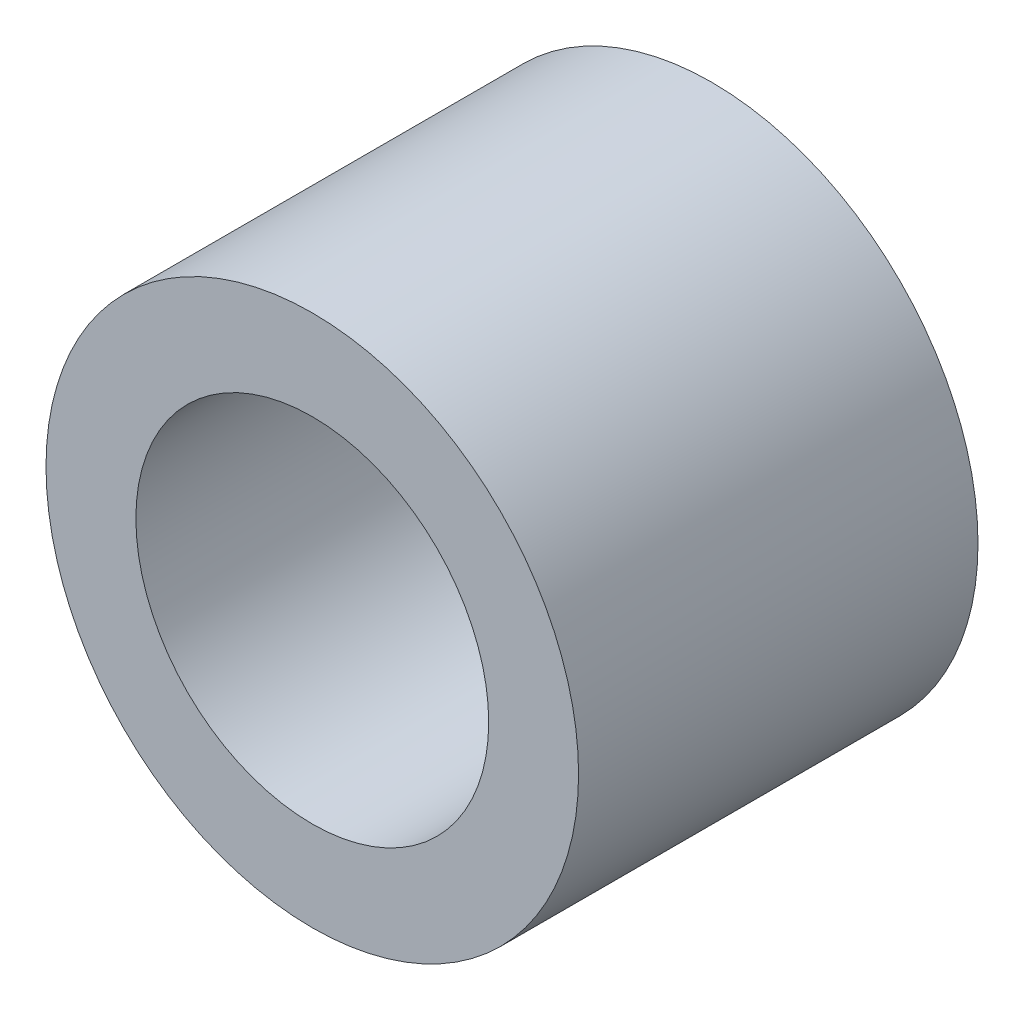
SolidWorks part; units mm, degrees
ref_plane "Front Plane" through (0, 0, 0) normal (0, 0, 1) x (1, 0, 0)
ref_plane "Top Plane" through (0, 0, 0) normal (0, 1, 0) x (1, 0, 0)
ref_plane "Right Plane" through (0, 0, 0) normal (1, 0, 0) x (0, 0, -1)
sketch "Sketch1" plane through (0, 0, 0) normal (0, 0, 1) x (1, 0, 0)
  line L0 (0, 2.65) -> (0, 4) construction
  line L1 (0, -2.65) -> (0, -4) construction
  circle A0 centre (0, 0) radius 4
  circle A1 centre (0, 0) radius 2.65
  dimension "OD" = 8
  dimension "ID" = 5.3
sketch "Sketch2" plane through (0, 0, 0) normal (1, 0, 0) x (0, 0, -1)
  line L0 (-3, 2.65) -> (3, 2.65) construction
  line L1 (-3, -2.65) -> (3, -2.65) construction
  line L2 (-3, -4) -> (3, -4) construction
  line L3 (-3, 4) -> (3, 4) construction
  dimension "Length" = 6
extrude "Extrude1" add sketch "Sketch1" along normal up to vertex (3 mm away) and the other way up to vertex (3 mm away) up to point (0, 2.65, 3) other way up to point (0, 2.65, -3)
sketch "Sketch3" plane through (0, 0, 3) normal (0, 0, 1) x (1, 0, 0)
  circle A0 centre (0, 0) radius 2.65 construction
  circle A3 centre (0, 0) radius 2.65
  point P3 (-2.65, 0)
